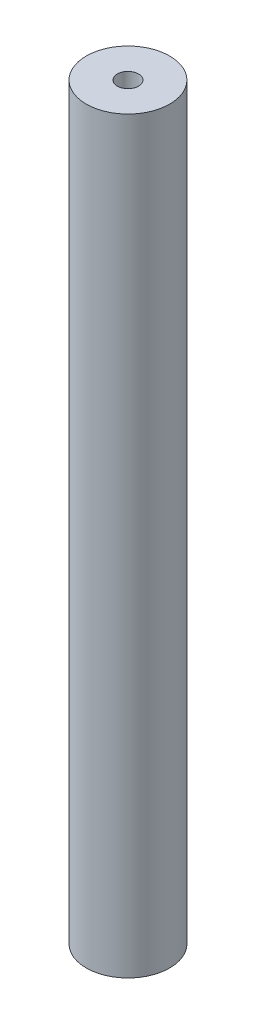
SolidWorks part; units mm, degrees
ref_plane "Front Plane" through (0, 0, 0) normal (0, 0, 1) x (1, 0, 0)
ref_plane "Top Plane" through (0, 0, 0) normal (0, 1, 0) x (1, 0, 0)
ref_plane "Right Plane" through (0, 0, 0) normal (1, 0, 0) x (0, 0, -1)
sketch "Sketch1" plane through (0, 0, 0) normal (0, 1, 0) x (1, 0, 0)
  circle A0 centre (0, 0) radius 4.445
  circle A1 centre (0, 0) radius 1.1303
  dimension "D1" = 8.89
  dimension "D2" = 2.2606
extrude "Boss-Extrude1" add sketch "Sketch1" along normal blind 79.756
